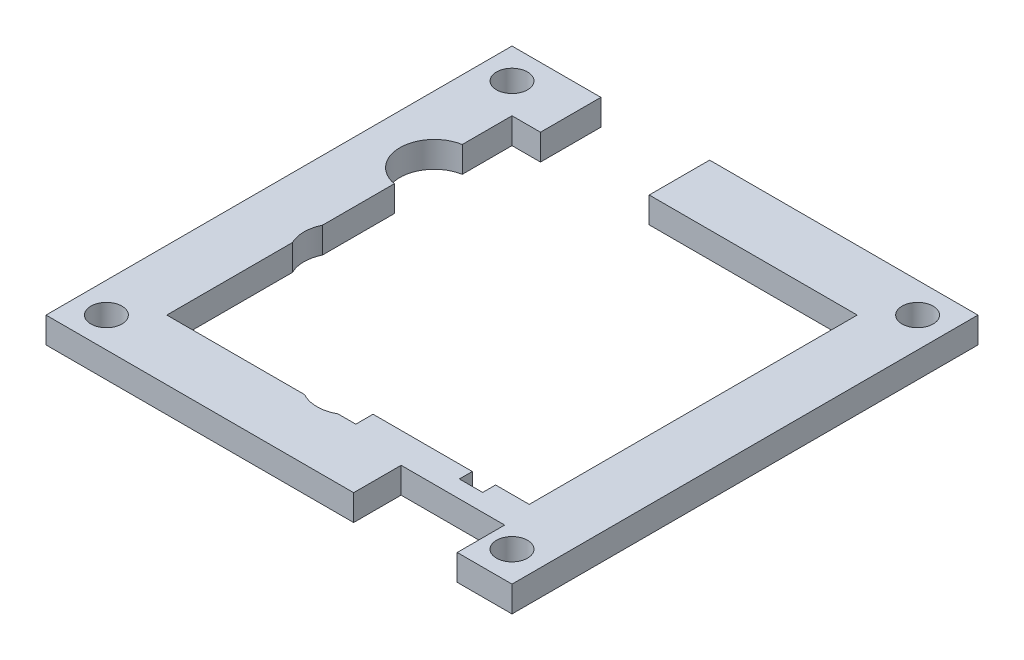
SolidWorks part; units mm, degrees
ref_plane "Front" through (0, 0, 0) normal (0, 0, 1) x (1, 0, 0)
ref_plane "Top" through (0, 0, 0) normal (0, 1, 0) x (1, 0, 0)
ref_plane "Right" through (0, 0, 0) normal (1, 0, 0) x (0, 0, -1)
sketch "草图3" plane through (0, 0, 0) normal (0, 1, 0) x (1, 0, 0)
  line L0 (16.9, -20) -> (20, -20)
  line L1 (-20, -20) -> (12.4, -20)
  line L2 (20, -20) -> (20, 20)
  line L3 (-27, 27) -> (-27, -27)
  line L4 (-27, -27) -> (27, -27)
  line L5 (27, -27) -> (27, 27)
  line L6 (27, 27) -> (-27, 27)
  line L7 (-8.6, 1.7) -> (-7.6812, 1.7)
  line L8 (-5.8437, 1.7) -> (-4.925, 1.7)
  line L9 (20.65, -20) -> (20, -20)
  line L10 (16.9, -6) -> (12.4, -6)
  line L11 (12.4, -6) -> (12.4, -19.5)
  line L12 (-10.4, 20) -> (-4.1, 20)
  line L13 (16.9, -6) -> (16.9, -19.5)
  line L14 (-20, 20) -> (-20, -20)
  line L15 (-3.0875, 1.7) -> (-2.1687, 1.7)
  line L16 (-0.3312, 1.7) -> (0.5875, 1.7)
  line L17 (2.425, 1.7) -> (3.3438, 1.7)
  line L18 (5.1813, 1.7) -> (6.1, 1.7)
  line L19 (8.8563, -13.3) -> (7.9375, -13.3)
  line L20 (8.65, -20) -> (8.65, -27)
  line L21 (-8.6, 1.7) -> (-8.6, -13.3)
  line L22 (-7.6812, -13.3) -> (-8.6, -13.3)
  line L23 (-8.6, -13.3) -> (-8.6029, -13.3589)
  line L24 (-10.4375, -13.3) -> (-11.3562, -13.3)
  line L25 (-10.4375, 1.7) -> (-11.3562, 1.7)
  line L26 (6.1, 1.7) -> (6.1, -13.3)
  line L27 (-4.925, -13.3) -> (-4.925, 1.7)
  line L28 (-11.3562, -13.3) -> (-11.3562, 1.7)
  line L29 (-3.0875, -13.3) -> (-3.0875, 1.7)
  line L30 (-10.4375, -13.3) -> (-10.4375, 1.7)
  line L31 (-2.1687, -13.3) -> (-2.1687, 1.7)
  line L32 (8.8563, 1.7) -> (7.9375, 1.7)
  line L33 (-5.8437, -13.3) -> (-5.8437, 1.7)
  line L34 (8.8563, -13.3) -> (8.8563, 1.7)
  line L35 (-7.6812, -13.3) -> (-7.6812, 1.7)
  line L36 (-0.3312, -13.3) -> (-0.3312, 1.7)
  line L37 (0.5875, -13.3) -> (0.5875, 1.7)
  line L38 (5.1813, -13.3) -> (6.1, -13.3)
  line L39 (2.425, -13.3) -> (2.425, 1.7)
  line L40 (3.3438, -13.3) -> (3.3438, 1.7)
  line L41 (2.425, -13.3) -> (3.3438, -13.3)
  line L42 (5.1813, -13.3) -> (5.1813, 1.7)
  line L43 (-0.3312, -13.3) -> (0.5875, -13.3)
  line L44 (-3.0875, -13.3) -> (-2.1687, -13.3)
  line L45 (-5.8437, -13.3) -> (-4.925, -13.3)
  line L46 (7.9375, -13.3) -> (7.9375, 1.7)
  line L47 (20.65, -20) -> (20.65, -27)
  line L48 (12.4, -19.5) -> (12.4, -20)
  line L49 (16.9, -19.5) -> (16.9, -20)
  line L50 (-20, -20) -> (20, -20) construction
  line L51 (-20, 20) -> (20, 20)
  line L52 (-16.7, 20) -> (-10.4, 20)
  line L53 (20, 20) -> (-20, 20) construction
  line L54 (-16.7, 20) -> (-16.7, 27)
  line L55 (-4.1, 20) -> (-4.1, 27)
  line L56 (12.4, -19.5) -> (16.9, -19.5)
  line L57 (1.9, -18) -> (12.4, -18)
  line L58 (8.65, -21.5) -> (20.65, -21.5)
  line L59 (1.9, -20) -> (1.9, -18)
  line L60 (16.9, -18) -> (16.1, -18)
  line L61 (16.9, -18) -> (20, -18)
  line L62 (12.4, -18) -> (13.4, -18)
  line L63 (13.4, -18) -> (13.4, -19.5)
  line L64 (16.1, -18) -> (16.1, -19.5)
  circle A0 centre (-23.5, -23.5) radius 1.8
  circle A1 centre (23.5, -23.5) radius 1.8
  circle A2 centre (-23.5, 23.5) radius 1.8
  circle A3 centre (23.5, 23.5) radius 1.8
  circle A4 centre (-2.1, -16.5) radius 2
  circle A5 centre (-16.4, -3.7) radius 2
  circle A6 centre (-19.3, 10.3) radius 2
  circle A7 centre (-1.1, 15.8) radius 2
  circle A8 centre (-19.3, 10.3) radius 4
  circle A9 centre (-2.1, -16.5) radius 4
  circle A10 centre (-1.1, 15.8) radius 4
  circle A11 centre (-16.4, -3.7) radius 4
  point P0 (0, 0)
  point P61 (-10.8969, 1.7)
  dimension "D1" = 7
extrude "凸台-拉伸2" add sketch "草图3" along normal blind 3 contours A11 L14 A8 L51 L54 L6 L3 L4 L20 L1 A9 A2 A0 | L55 L51 L2 L9 L47 L4 L5 L6 A3 A1 | L59 L1 L48 L11 L57 | L20 L58 L47 L9 L0 L49 L56 L48 L1 | L61 L13 L49 L0 L2 | L60 L64 L56 L13 | L63 L62 L11 L56
